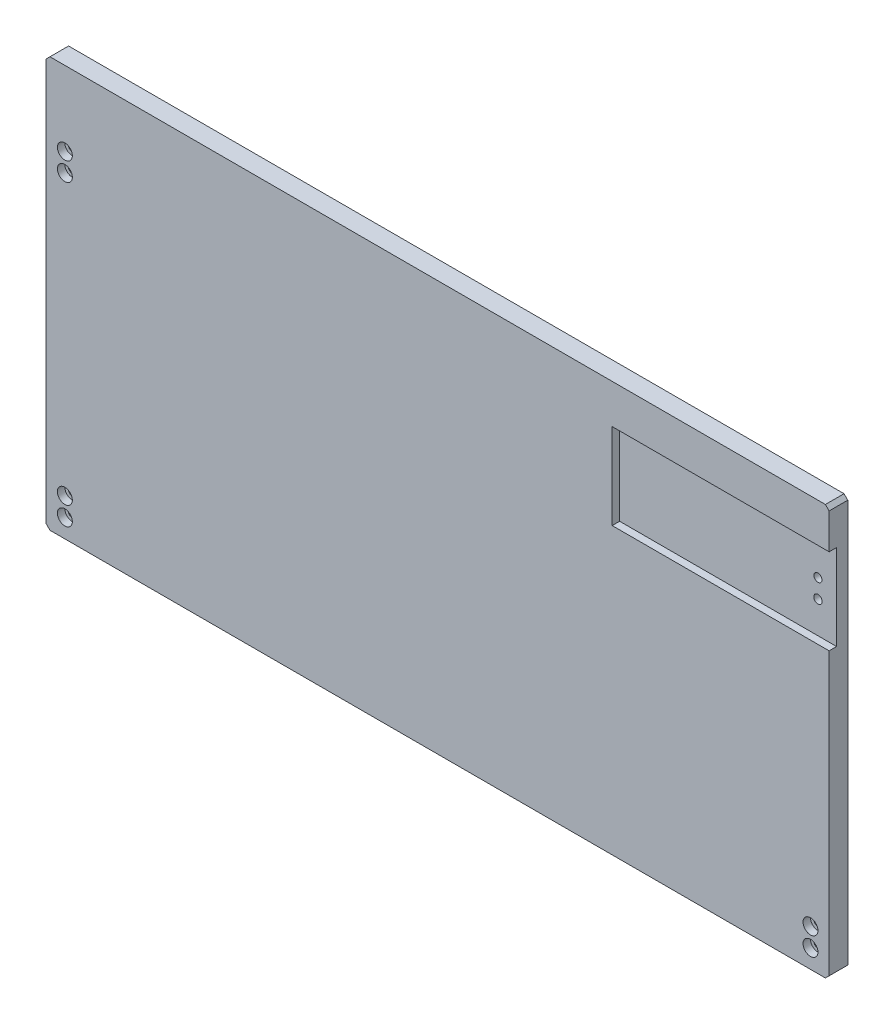
SolidWorks part; units mm, degrees
ref_plane "Front Plane" through (0, 0, 0) normal (0, 0, 1) x (1, 0, 0)
ref_plane "Top Plane" through (0, 0, 0) normal (0, 1, 0) x (1, 0, 0)
ref_plane "Right Plane" through (0, 0, 0) normal (1, 0, 0) x (0, 0, -1)
sketch "Sketch1" plane through (0, 0, 0) normal (0, 0, 1) x (1, 0, 0)
  line L1 (-210, -110) -> (210, -110)
  line L2 (-210, -110) -> (-210, 110)
  line L3 (-210, 110) -> (210, 110)
  line L4 (210, -110) -> (210, 110)
  line L5 (-210, -110) -> (210, 110) construction
  line L6 (-210, 110) -> (210, -110) construction
  point P0 (0, 0)
  dimension "D1" = 220
  dimension "D2" = 420
extrude "Boss-Extrude1" add sketch "Sketch1" along normal blind 10
sketch "Sketch2" plane through (0, 0, 10) normal (0, 0, 1) x (1, 0, 0)
  line L0 (-259.8524, 60) -> (266.8628, 60) construction
  line L1 (0, 159.1362) -> (0, -140.4418) construction
  line L2 (-210, -110) -> (210, -110) construction
  line L3 (210, 110) -> (-210, 110) construction
  line L4 (-210, 110) -> (-210, -110) construction
  circle A0 centre (-200, 60) radius 2.25
  circle A1 centre (200, 60) radius 2.25
  circle A2 centre (200, -100) radius 2.25
  circle A3 centre (-200, -100) radius 2.25
  dimension "D3" = 4.5
  dimension "D1" = 50
  dimension "D2" = 200
  dimension "D4" = 200
  dimension "D5" = 10
  dimension "D6" = 10
extrude "Cut-Extrude1" cut sketch "Sketch2" against normal blind 10
sketch "Sketch3" plane through (0, 0, 10) normal (0, 0, 1) x (1, 0, 0)
  circle A0 centre (-200, 60) radius 4
  circle A1 centre (-200, -100) radius 4
  circle A2 centre (200, 60) radius 4
  circle A3 centre (200, -100) radius 4
  dimension "D1" = 8
extrude "Cut-Extrude2" cut sketch "Sketch3" against normal blind 4
chamfer "Chamfer1" distance 2 angle 45 4 edges at (-210, -110, 5) (-210, 110, 5) (210, 110, 5) (210, -110, 5)
sketch "Sketch5" plane through (210, 0, 0) normal (1, 0, 0) x (0, 0, -1)
  line L0 (-10, -108) -> (-10, 108) construction
  line L1 (-10, 89) -> (-6, 89)
  line L2 (-10, 89) -> (-10, 43)
  line L3 (-10, 43) -> (-6, 43)
  line L4 (-6, 89) -> (-6, 43)
  line L5 (-10, 110) -> (0, 110) construction
  line L6 (0, -110) -> (-10, -110) construction
  point P10 (-8, 43)
  dimension "D1" = 46
  dimension "D2" = 4
  dimension "D3" = 21
  dimension "D4" = 67
  dimension "D5" = 153
extrude "Cut-Extrude3" cut sketch "Sketch5" against normal blind 116.38
sketch "Sketch6" plane through (0, 0, 10) normal (0, 0, 1) x (1, 0, 0)
  line L0 (-252.6044, 66) -> (260.8152, 66) construction
  line L2 (-208, -110) -> (208, -110) construction
  circle A0 centre (-200, -100) radius 10 construction
  dimension "D1" = 20
  dimension "D2" = 176
sketch "Sketch7" plane through (0, 0, 10) normal (0, 0, 1) x (1, 0, 0)
  line L0 (-200, -100) -> (-200, 120.4479) construction
  line L1 (200, -100) -> (200, 134.5273) construction
  circle A0 centre (200, -90) radius 2.15
  circle A1 centre (200, 70) radius 2.15
  circle A2 centre (-200, -90) radius 2.15
  circle A3 centre (-200, 70) radius 2.15
  point P14 (200, 60)
  point P15 (-200, 60)
  dimension "D1" = 4.3
  dimension "D2" = 10
  dimension "D3" = 10
  dimension "D4" = 160
extrude "Cut-Extrude4" cut sketch "Sketch7" against normal through all
sketch "Sketch8" plane through (0, 0, 10) normal (0, 0, 1) x (1, 0, 0)
  circle A0 centre (-200, 70) radius 4
  circle A1 centre (-200, -90) radius 4
  circle A2 centre (200, -90) radius 4
  dimension "D1" = 8
extrude "Cut-Extrude5" cut sketch "Sketch8" against normal blind 4
